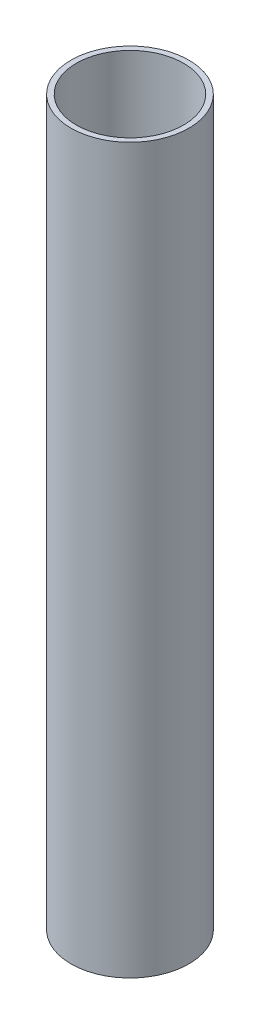
SolidWorks part; units mm, degrees
ref_plane "前视基准面" through (0, 0, 0) normal (0, 0, 1) x (1, 0, 0)
ref_plane "上视基准面" through (0, 0, 0) normal (0, 1, 0) x (1, 0, 0)
ref_plane "右视基准面" through (0, 0, 0) normal (1, 0, 0) x (0, 0, -1)
sketch "草图1" plane through (0, 0, 0) normal (0, 1, 0) x (1, 0, 0)
  circle A0 centre (0, 0) radius 11
  circle A1 centre (0, 0) radius 10
  dimension "D1" = 20
  dimension "D2" = 22
extrude "凸台-拉伸1" add sketch "草图1" along normal blind 135 contours A1 | A0
